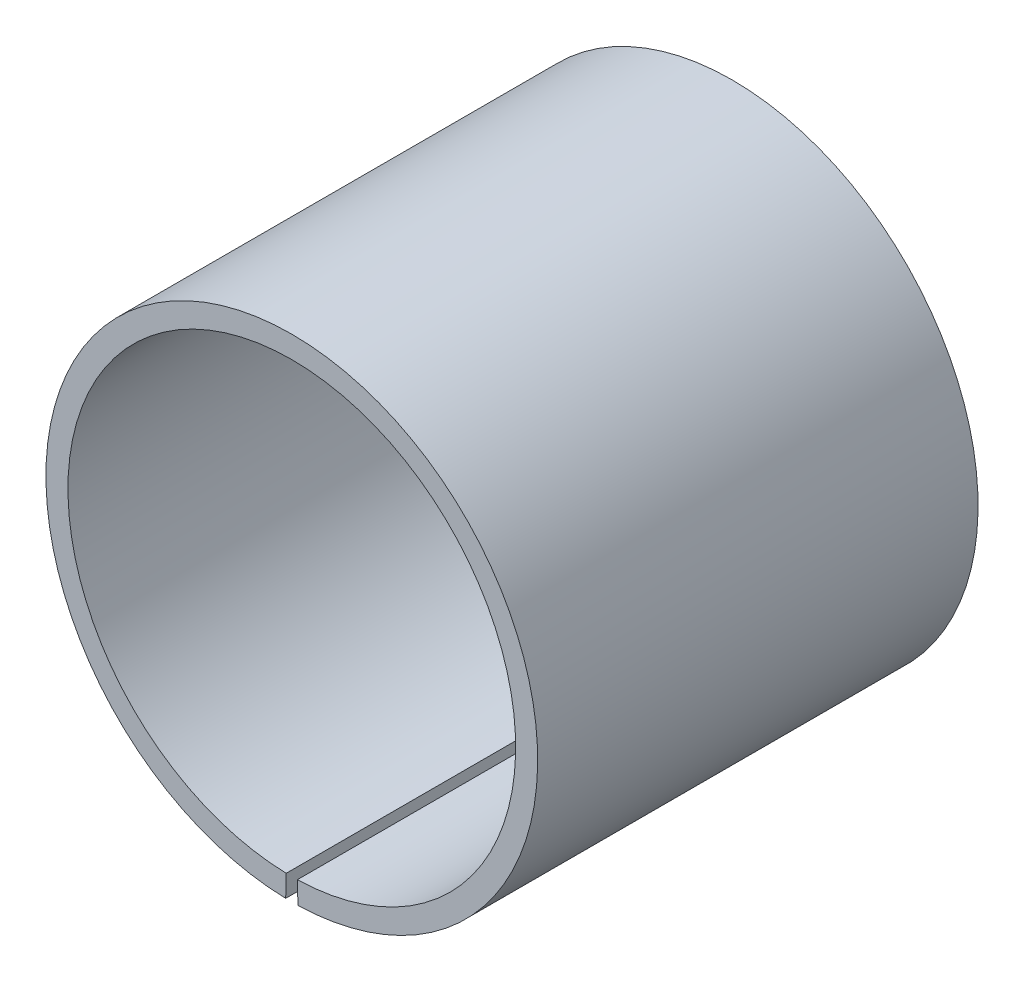
SolidWorks part; units mm, degrees
ref_plane "前视基准面" through (0, 0, 0) normal (0, 0, 1) x (1, 0, 0)
ref_plane "上视基准面" through (0, 0, 0) normal (0, 1, 0) x (1, 0, 0)
ref_plane "右视基准面" through (0, 0, 0) normal (1, 0, 0) x (0, 0, -1)
other "Configuration Table"
sketch "Sketch1" plane through (0, 0, 0) normal (0, 0, 1) x (1, 0, 0)
  line L2 (-0.3797, -15.2453) -> (-0.4171, -16.7448)
  line L4 (0.4171, -16.7448) -> (0.3797, -15.2453)
  arc A0 (0.3797, -15.2453) -> (-0.3797, -15.2453) centre (0, 0) ccw
  arc A1 (0.4171, -16.7448) -> (-0.4171, -16.7448) centre (0, 0) ccw
  dimension "D1" = 1.5
  dimension "D2" = 30.5
extrude "Boss-Extrude1" add sketch "Sketch1" along normal mid plane 30
